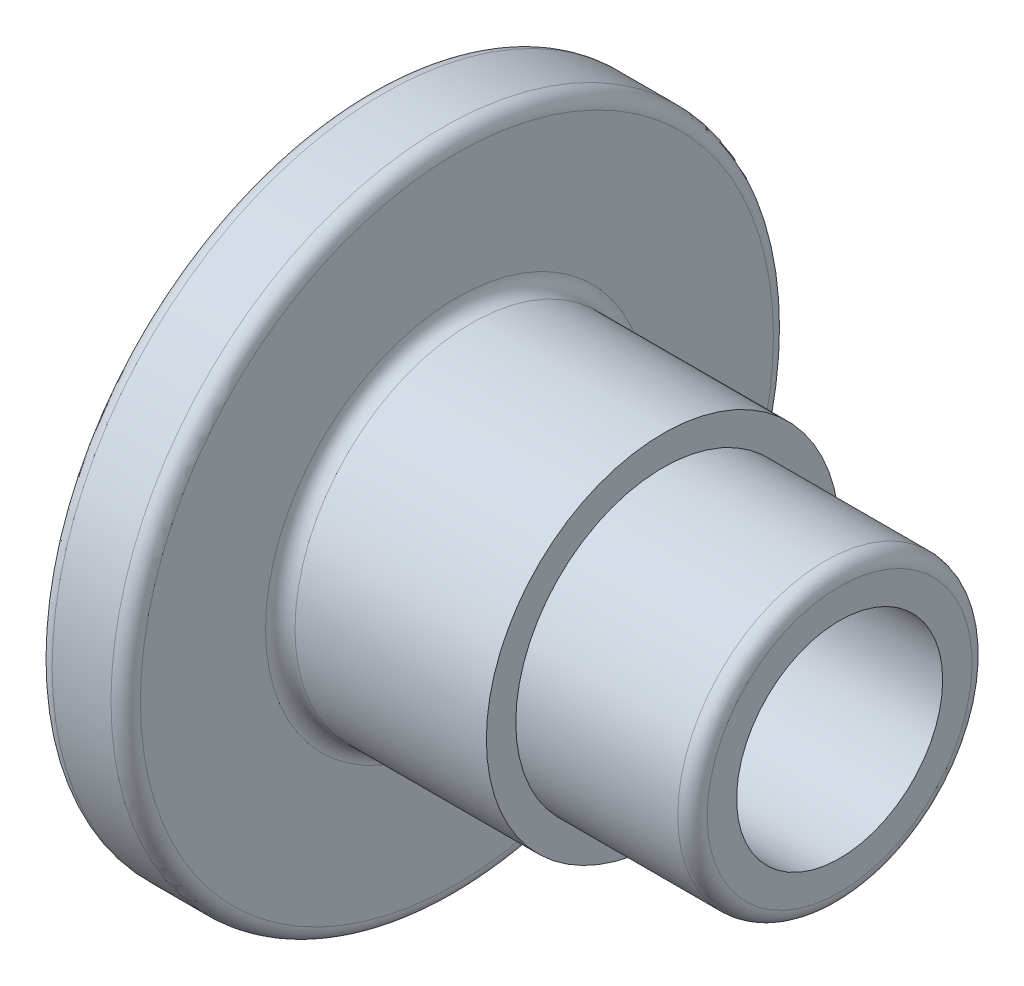
SolidWorks part; units mm, degrees
material "Plain Carbon Steel"
ref_plane "Front Plane" through (0, 0, 0) normal (0, 0, 1) x (1, 0, 0)
ref_plane "Top Plane" through (0, 0, 0) normal (0, 1, 0) x (1, 0, 0)
ref_plane "Right Plane" through (0, 0, 0) normal (1, 0, 0) x (0, 0, -1)
sketch "Sketch1" plane through (0, 0, 0) normal (0, 0, 1) x (1, 0, 0)
  line L0 (0, 0) -> (88.7628, 0) construction
  line L1 (0, 0) -> (0, 11.25)
  line L2 (0, 11.25) -> (3, 11.25)
  line L3 (3, 11.25) -> (3, 6)
  line L4 (3, 6) -> (10, 6)
  line L5 (10, 6) -> (10, 5)
  line L6 (10, 5) -> (16, 5)
  line L7 (16, 5) -> (16, 0)
  line L8 (16, 0) -> (0, 0)
  dimension "D1" = 3
  dimension "D2" = 7
  dimension "D3" = 6
  dimension "D4" = 11.25
  dimension "D5" = 6
  dimension "D6" = 5
revolve "Revolve1" add sketch "Sketch1" angle 360 about L0
fillet "Fillet1" radius 0.5 4 edges at (16, 0, 5) (0, 0, 11.25) (3, 0, 11.25) (3, 0, 6)
hole_wizard "M8x1.0 Tapped Hole1" positions "Sketch3" profile "Sketch2" tap size "M8x1.0" standard "Ansi Metric" end condition through all
sketch "Sketch3" plane through (16, 0, 0) normal (1, 0, 0) x (0, 0, -1)
  circle A0 centre (0, 0) radius 4.5 construction
  point P0 (0, 0)
sketch "Sketch2" plane through (16, 0, 0) normal (0, 1, 0) x (0, 0, -1)
  line L0 (0, 0) -> (0, 16)
  line L1 (0, 16) -> (3.5, 16)
  line L2 (3.5, 16) -> (3.5, 0)
  line L5 (3.5, 0) -> (0, 0)
  line L11 (0, -6.35) -> (0, 107.95) construction
  dimension "Thru Tap Drill Dia." = 7
  dimension "Thru Tap Drill Depth" = 16
cosmetic thread "Hole Thread1" parameters "D2"=8
sketch "Sketch4" plane through (0, 0, 0) normal (-1, 0, 0) x (0, 0, 1)
  circle A0 centre (0, 0) radius 5
  dimension "D1" = 10
extrude "Cut-Extrude1" cut sketch "Sketch4" against normal blind 5
